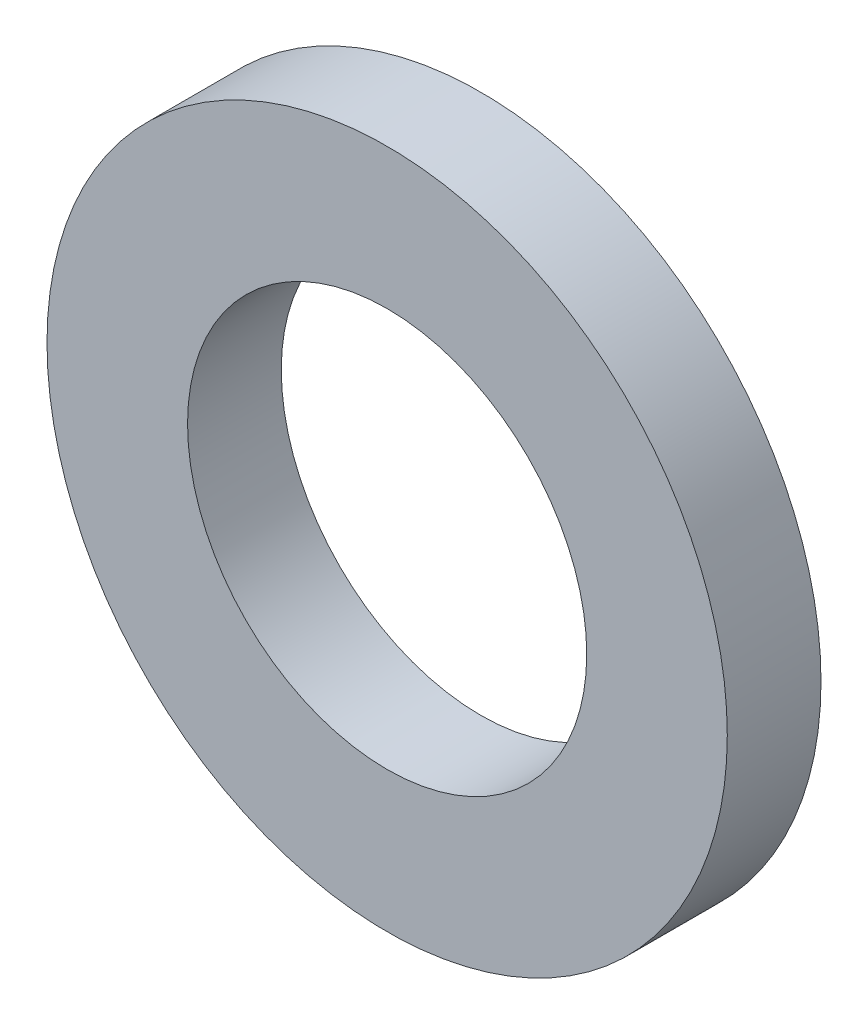
SolidWorks part; units mm, degrees
ref_plane "Front" through (0, 0, 0) normal (0, 0, 1) x (1, 0, 0)
ref_plane "Top" through (0, 0, 0) normal (0, 1, 0) x (1, 0, 0)
ref_plane "Right" through (0, 0, 0) normal (1, 0, 0) x (0, 0, -1)
sketch "Sketch1" plane through (0, 0, 0) normal (0, 0, 1) x (1, 0, 0)
  circle A0 centre (0, 0) radius 21.3
  circle A1 centre (0, 0) radius 36.3
  dimension "D1" = 42.6
  dimension "D2" = 15
extrude "Boss-Extrude1" add sketch "Sketch1" along normal blind 10
